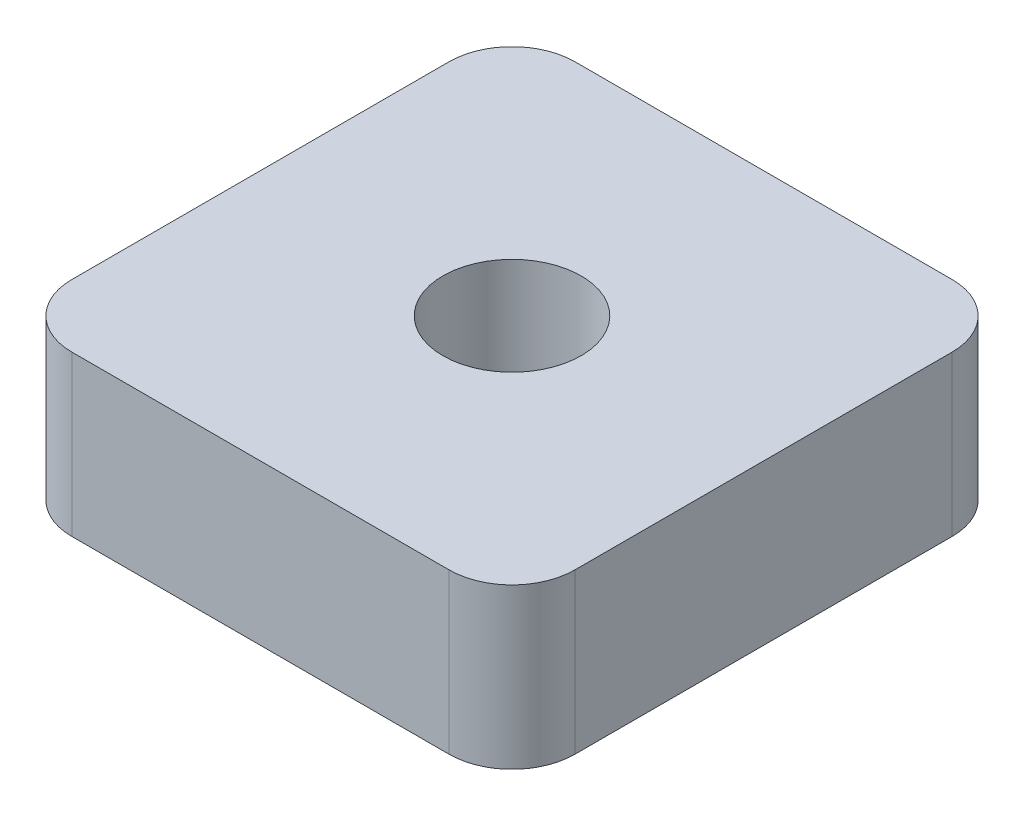
SolidWorks part; units mm, degrees
ref_plane "Front Plane" through (0, 0, 0) normal (0, 0, 1) x (1, 0, 0)
ref_plane "Top Plane" through (0, 0, 0) normal (0, 1, 0) x (1, 0, 0)
ref_plane "Right Plane" through (0, 0, 0) normal (1, 0, 0) x (0, 0, -1)
sketch "Sketch1" plane through (0, 0, 0) normal (0, 1, 0) x (1, 0, 0)
  line L1 (-10, -10) -> (10, -10)
  line L2 (-10, -10) -> (-10, 10)
  line L3 (-10, 10) -> (10, 10)
  line L4 (10, -10) -> (10, 10)
  line L5 (-10, -10) -> (10, 10) construction
  line L6 (-10, 10) -> (10, -10) construction
  point P0 (0, 0)
  dimension "D1" = 20
extrude "Boss-Extrude1" add sketch "Sketch1" along normal blind 6.35
hole_wizard "M5 Clearance Hole1" positions "Sketch2" profile "Sketch3" hole size "M5" standard "ANSI Metric" end condition through all
sketch "Sketch2" plane through (0, 6.35, 0) normal (0, 1, 0) x (1, 0, 0)
  point P0 (0, 0)
sketch "Sketch3" plane through (0, 6.35, 0) normal (1, 0, 0) x (0, 0, 1)
  line L0 (0, 0) -> (0, 6.35)
  line L1 (0, 6.35) -> (2.75, 6.35)
  line L2 (2.75, 6.35) -> (2.75, 0)
  line L5 (2.75, 0) -> (0, 0)
  line L11 (0, -6.35) -> (0, 107.95) construction
  dimension "Thru Hole Dia." = 5.5
  dimension "Thru Hole Depth" = 6.35
fillet "Fillet1" radius 2.5 4 edges at (10, 3.175, 10) (-10, 3.175, -10) (10, 3.175, -10) (-10, 3.175, 10)
